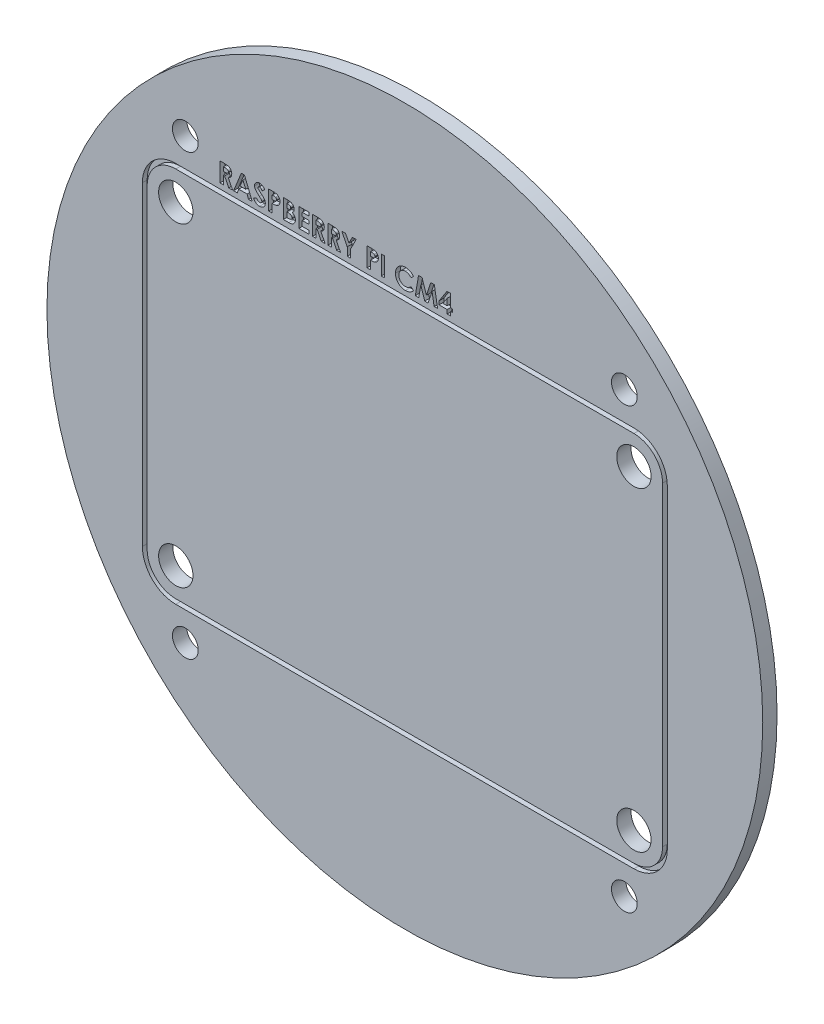
SolidWorks part; units mm, degrees
ref_plane "Plan de face" through (0, 0, 0) normal (0, 0, 1) x (1, 0, 0)
ref_plane "Plan de dessus" through (0, 0, 0) normal (0, 1, 0) x (1, 0, 0)
ref_plane "Plan de droite" through (0, 0, 0) normal (1, 0, 0) x (0, 0, -1)
sketch "Esquisse1" plane through (0, 0, 0) normal (0, 0, 1) x (1, 0, 0)
  line L1 (-23, -23) -> (23, -23) construction
  line L2 (-23, -23) -> (-23, 23) construction
  line L3 (-23, 23) -> (23, 23) construction
  line L4 (23, -23) -> (23, 23) construction
  line L5 (-23, -23) -> (23, 23) construction
  line L6 (-23, 23) -> (23, -23) construction
  line L7 (-24, -16.5) -> (24, -16.5) construction
  line L8 (-24, -16.5) -> (-24, 16.5) construction
  line L9 (-24, 16.5) -> (24, 16.5) construction
  line L10 (24, -16.5) -> (24, 16.5) construction
  line L11 (-24, -16.5) -> (24, 16.5) construction
  line L12 (-24, 16.5) -> (24, -16.5) construction
  circle A0 centre (0, 0) radius 37.5
  dimension "D3" = 75
  dimension "D1" = 48
  dimension "D2" = 46
  dimension "D4" = 33
extrude "Boss.-Extru.1" add sketch "Esquisse1" along normal blind 1.5
hole_wizard "Dégagement M2.51" positions "Esquisse2" profile "Esquisse3" hole size "M2.5" standard "ISO" end condition through all
sketch "Esquisse2" plane through (0, 0, 1.5) normal (0, 0, 1) x (1, 0, 0)
  point P0 (-23, 23)
  point P3 (23, 23)
  point P6 (23, -23)
  point P9 (-23, -23)
sketch "Esquisse3" plane through (-23, 23, 1.5) normal (1, 0, 0) x (0, -1, 0)
  line L0 (0, 0) -> (0, 1.5)
  line L1 (0, 1.5) -> (1.35, 1.5)
  line L2 (1.35, 1.5) -> (1.35, 0)
  line L5 (1.35, 0) -> (0, 0)
  line L11 (0, -6.35) -> (0, 107.95) construction
  dimension "Diamètre du perçage jusqu'au prochain" = 2.7
  dimension "Profondeur du perçage jusqu'au prochain" = 1.5
hole_wizard "Dégagement M31" positions "Esquisse4" profile "Esquisse5" hole size "M3" standard "ISO" end condition through all
sketch "Esquisse4" plane through (0, 0, 1.5) normal (0, 0, 1) x (1, 0, 0)
  point P0 (-24, 16.5)
  point P3 (24, 16.5)
  point P6 (24, -16.5)
  point P9 (-24, -16.5)
sketch "Esquisse5" plane through (-24, 16.5, 1.5) normal (1, 0, 0) x (0, -1, 0)
  line L0 (0, 0) -> (0, 1.5)
  line L1 (0, 1.5) -> (1.8, 1.5)
  line L2 (1.8, 1.5) -> (1.8, 0)
  line L5 (1.8, 0) -> (0, 0)
  line L11 (0, -6.35) -> (0, 107.95) construction
  dimension "Diamètre du perçage jusqu'au prochain" = 3.6
  dimension "Profondeur du perçage jusqu'au prochain" = 1.5
sketch "Esquisse6" plane through (0, 0, 1.5) normal (0, 0, 1) x (1, 0, 0)
  line L0 (-27.5, 16.5) -> (-27.5, -16.5)
  line L1 (-24, 19.5) -> (24, 19.5)
  line L2 (-27, 16.5) -> (-27, -16.5)
  line L3 (-24, -19.5) -> (24, -19.5)
  line L4 (27, 16.5) -> (27, -16.5)
  line L5 (-27, 19.5) -> (27, -19.5) construction
  line L6 (-27, -19.5) -> (27, 19.5) construction
  line L7 (-24, -20) -> (24, -20)
  line L8 (27.5, 16.5) -> (27.5, -16.5)
  line L9 (-24, 20) -> (24, 20)
  arc A0 (-27, -16.5) -> (-24, -19.5) centre (-24, -16.5) ccw
  arc A1 (24, -19.5) -> (27, -16.5) centre (24, -16.5) ccw
  arc A2 (24, 19.5) -> (27, 16.5) centre (24, 16.5) cw
  arc A3 (-24, 19.5) -> (-27, 16.5) centre (-24, 16.5) ccw
  circle A4 centre (-24, 16.5) radius 1.8 construction
  arc A5 (-27.5, -16.5) -> (-24, -20) centre (-24, -16.5) ccw
  arc A6 (24, -20) -> (27.5, -16.5) centre (24, -16.5) ccw
  arc A7 (24, 20) -> (27.5, 16.5) centre (24, 16.5) cw
  arc A8 (-24, 20) -> (-27.5, 16.5) centre (-24, 16.5) ccw
  point P0 (0, 0)
  dimension "D1" = 3
  dimension "D2" = 0.5
extrude "Enlèv. mat.-Extru.1" cut sketch "Esquisse6" against normal blind 0.5
sketch "Esquisse7" plane through (0, 0, 1.5) normal (0, 0, 1) x (1, 0, 0)
  line L0 (-19.5963, 20.5548) -> (17.9051, 20.5548) construction
  text T0 "<b>RASPBERRY PI CM4</b>" font "Century Gothic" height 2
extrude "Enlèv. mat.-Extru.2" cut sketch "Esquisse7" against normal blind 0.5
